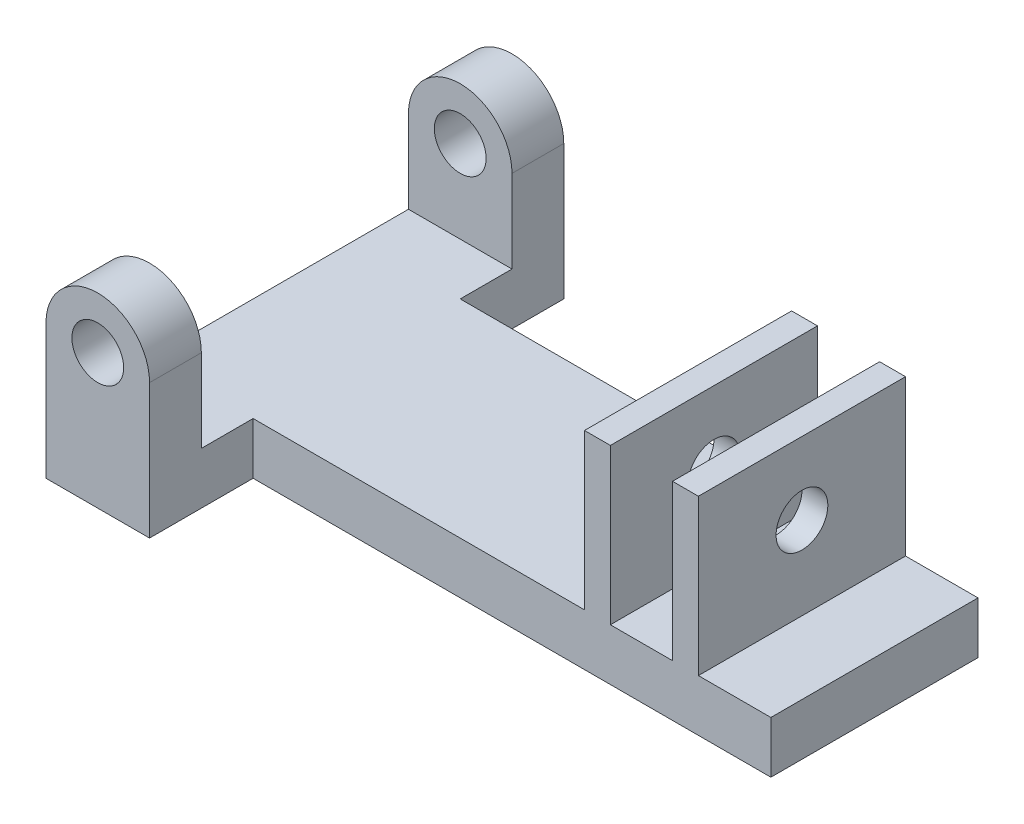
SolidWorks part; units mm, degrees
ref_plane "Front Plane" through (0, 0, 0) normal (0, 0, 1) x (1, 0, 0)
ref_plane "Top Plane" through (0, 0, 0) normal (0, 1, 0) x (1, 0, 0)
ref_plane "Right Plane" through (0, 0, 0) normal (1, 0, 0) x (0, 0, -1)
sketch "Sketch1" plane through (0, 0, 0) normal (0, 1, 0) x (1, 0, 0)
  line L1 (-12.7, 0) -> (0, 0)
  line L2 (-12.7, 0) -> (-12.7, 50.8)
  line L3 (-12.7, 50.8) -> (0, 50.8)
  line L4 (0, 0) -> (0, 50.8)
  line L5 (-12.7, 0) -> (0, 50.8) construction
  line L6 (-12.7, 50.8) -> (0, 0) construction
  point P0 (-6.35, 25.4)
  dimension "D1" = 12.7
  dimension "D2" = 50.8
extrude "Base Extrude" add sketch "Sketch1" along normal blind 6.35
sketch "Sketch6" plane through (0, 6.35, 0) normal (0, 1, 0) x (1, 0, 0)
  line L0 (0, 0) -> (0, 50.8) construction
  line L1 (-12.7, 0) -> (0, 0)
  line L2 (-12.7, 0) -> (-12.7, 6.35)
  line L3 (-12.7, 6.35) -> (0, 6.35)
  line L4 (0, 0) -> (0, 6.35)
  dimension "D1" = 6.35
extrude "Arch Base Extrude" add sketch "Sketch6" along normal blind 10.16
ref_plane "Arch Mirror Plane" through (0, 0, -25.4) normal (0, 0, 1) x (1, 0, 0)
mirror "Mirror Arch Base" about plane through (0, 0, -25.4) normal (0, 0, 1) of "Arch Base Extrude"
sketch "Sketch2" plane through (0, 0, 0) normal (0, 0, 1) x (1, 0, 0)
  line L1 (-12.7, 16.51) -> (0, 16.51)
  arc A1 (-12.7, 16.51) -> (0, 16.51) centre (-6.35, 16.51) cw
extrude "Arch Extrude" add sketch "Sketch2" against normal blind 6.35
sketch "Sketch3" plane through (0, 0, 0) normal (0, 0, 1) x (1, 0, 0)
  line L0 (-12.7, 0) -> (0, 0) construction
  circle A0 centre (-6.35, 16.51) radius 3.175
  arc A1 (0, 16.51) -> (-12.7, 16.51) centre (-6.35, 16.51) ccw construction
  point P5 (-6.35, 0)
  point P9 (-6.35, 22.86)
  dimension "D1" = 6.35
  dimension "D2" = 6.35
extrude "Arch Hole Cut" cut sketch "Sketch3" against normal up to surface (6.35 mm away) up to face at (-6.35, 13.0175, -6.35)
mirror "Mirror Arch and Hole" about plane through (0, 0, -25.4) normal (0, 0, 1) of "Arch Extrude", "Arch Hole Cut"
sketch "Sketch4" plane through (0, 0, 0) normal (1, 0, 0) x (0, 0, -1)
  line L0 (6.35, 6.35) -> (44.45, 6.35) construction
  line L1 (12.7, 6.35) -> (38.1, 6.35)
  line L2 (12.7, 6.35) -> (12.7, 0)
  line L3 (12.7, 0) -> (38.1, 0)
  line L4 (38.1, 6.35) -> (38.1, 0)
  line L5 (0, 0) -> (50.8, 0) construction
  point P8 (25.4, 0)
  dimension "D1" = 25.4
extrude "Tab Extrude" add sketch "Sketch4" along normal blind 63.5
sketch "Sketch5" plane through (0, 6.35, 0) normal (0, 1, 0) x (1, 0, 0)
  line L0 (63.5, 38.1) -> (0, 38.1) construction
  line L1 (40.64, 38.1) -> (43.815, 38.1)
  line L2 (40.64, 38.1) -> (40.64, 12.7)
  line L3 (40.64, 12.7) -> (43.815, 12.7)
  line L4 (43.815, 38.1) -> (43.815, 12.7)
  line L5 (63.5, 12.7) -> (0, 12.7) construction
  line L6 (0, 6.35) -> (0, 12.7) construction
  line L8 (54.61, 38.1) -> (51.435, 38.1)
  line L9 (54.61, 38.1) -> (54.61, 12.7)
  line L10 (54.61, 12.7) -> (51.435, 12.7)
  line L11 (51.435, 38.1) -> (51.435, 12.7)
  dimension "D1" = 40.64
  dimension "D2" = 3.175
  dimension "D3" = 3.175
  dimension "D4" = 7.62
extrude "Square Slide Guides Extrude" add sketch "Sketch5" along normal blind 19.05
sketch "Sketch14" plane through (54.61, 0, 0) normal (1, 0, 0) x (0, 0, -1)
  line L0 (12.7, 6.35) -> (38.1, 6.35) construction
  circle A0 centre (25.4, 16.51) radius 3.175
  point P4 (25.4, 6.35)
  dimension "D2" = 6.35
  dimension "D1" = 10.16
extrude "Cut-Extrude3" cut sketch "Sketch14" against normal up to surface (13.97 mm away) up to face at (40.64, 15.875, -25.4)
